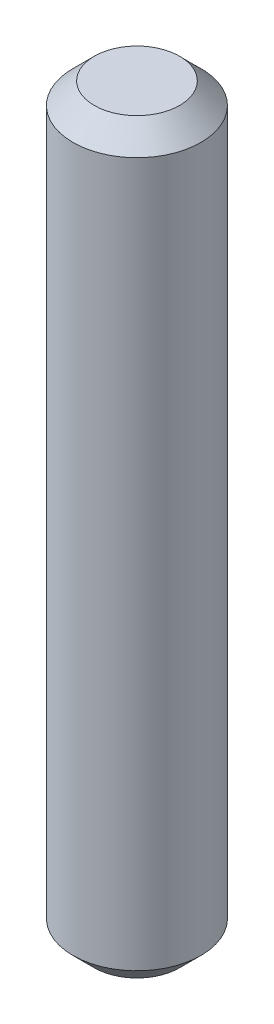
SolidWorks part; units mm, degrees
ref_plane "Front Plane" through (0, 0, 0) normal (0, 0, 1) x (1, 0, 0)
ref_plane "Top Plane" through (0, 0, 0) normal (0, 1, 0) x (1, 0, 0)
ref_plane "Right Plane" through (0, 0, 0) normal (1, 0, 0) x (0, 0, -1)
sketch "Sketch1" plane through (0, 0, 0) normal (0, 1, 0) x (1, 0, 0)
  circle A0 centre (0, 0) radius 6
  dimension "D1" = 12
extrude "Boss-Extrude1" add sketch "Sketch1" along normal blind 70
chamfer "Chamfer1" distance 2 angle 45 2 edges at (0, 0, 6) (0, 70, 6)
cosmetic thread "Cosmetic Thread3" parameters "D1"=14, "D2"=10.072
cosmetic thread "Cosmetic Thread4" parameters "D1"=40, "D2"=10.072
